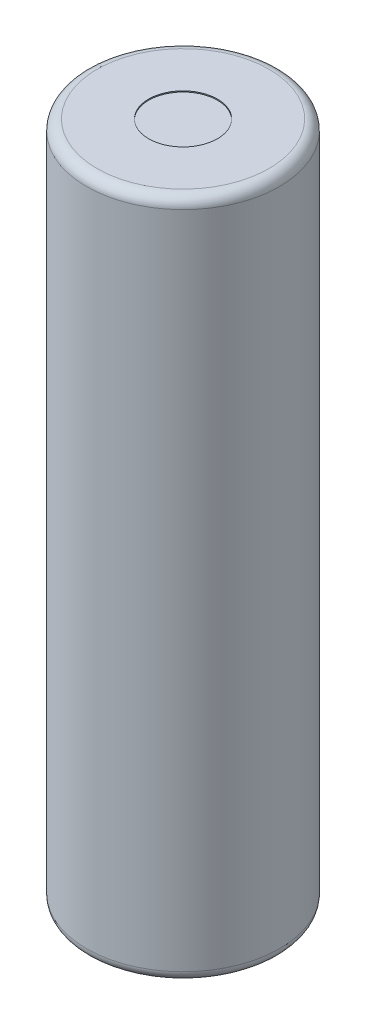
SolidWorks part; units mm, degrees
ref_plane "Front Plane" through (0, 0, 0) normal (0, 0, 1) x (1, 0, 0)
ref_plane "Top Plane" through (0, 0, 0) normal (0, 1, 0) x (1, 0, 0)
ref_plane "Right Plane" through (0, 0, 0) normal (1, 0, 0) x (0, 0, -1)
sketch "Sketch2" plane through (0, 0, 0) normal (0, 1, 0) x (1, 0, 0)
  circle A0 centre (0, 0) radius 9.25
  dimension "D1" = 18.5
extrude "Boss-Extrude1" add sketch "Sketch2" along normal mid plane 65.3
fillet "Fillet1" radius 1 2 edges at (0, -32.65, 9.25) (0, 32.65, 9.25)
sketch "Sketch3" plane through (0, 32.65, 0) normal (0, 1, 0) x (1, 0, 0)
  circle A0 centre (0, 0) radius 3.3
  dimension "D1" = 6.6
extrude "Cut-Extrude1" cut sketch "Sketch3" against normal blind 0.1
sketch "Sketch4" plane through (0, -32.65, 0) normal (0, -1, 0) x (1, 0, 0)
  circle A0 centre (0, 0) radius 3.3
  dimension "D1" = 6.6
extrude "Boss-Extrude2" add sketch "Sketch4" along normal blind 0.5
fillet "Fillet2" radius 0.25 1 edges at (0, -33.15, -3.3)
